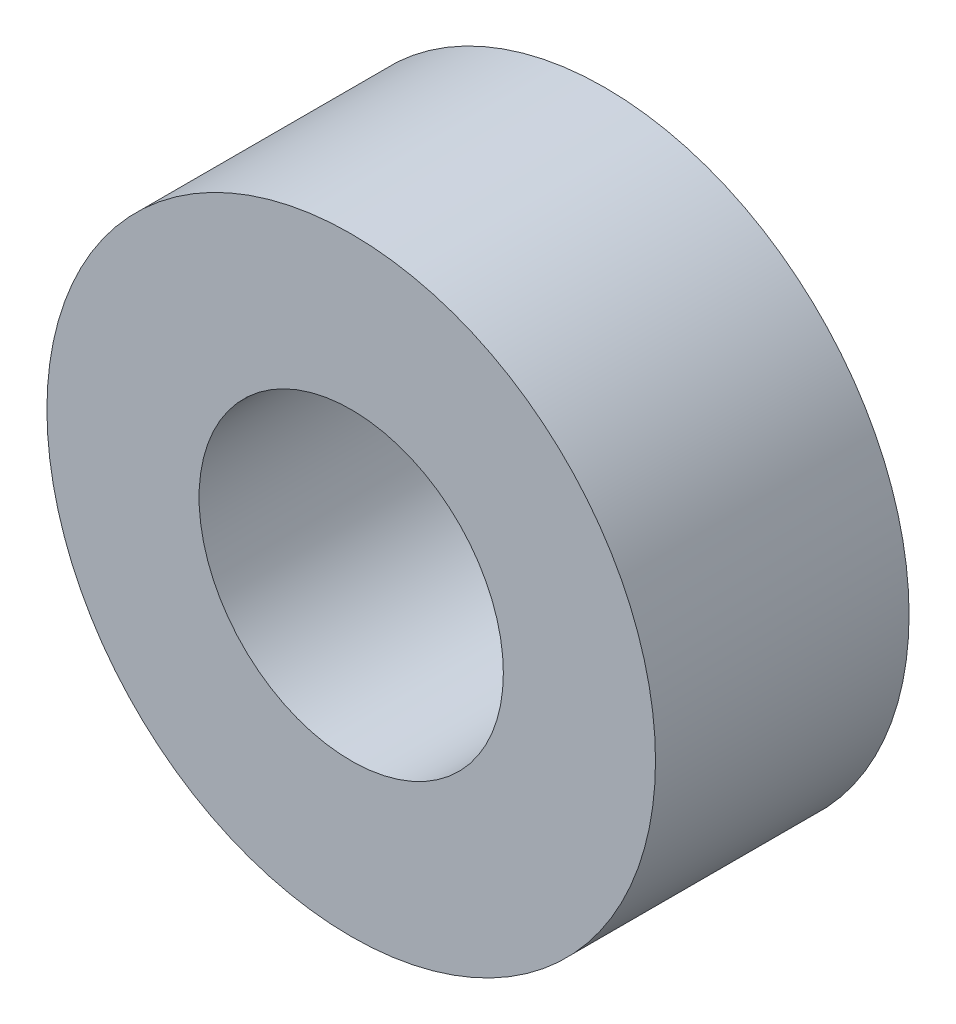
SolidWorks part; units mm, degrees
ref_plane "Front Plane" through (0, 0, 0) normal (0, 0, 1) x (1, 0, 0)
ref_plane "Top Plane" through (0, 0, 0) normal (0, 1, 0) x (1, 0, 0)
ref_plane "Right Plane" through (0, 0, 0) normal (1, 0, 0) x (0, 0, -1)
sketch "Sketch1" plane through (0, 0, 0) normal (0, 0, 1) x (1, 0, 0)
  circle A0 centre (0, 0) radius 1.5
  circle A1 centre (0, 0) radius 3
  dimension "D1" = 3
  dimension "D2" = 6
extrude "Boss-Extrude1" add sketch "Sketch1" along normal blind 2.5
